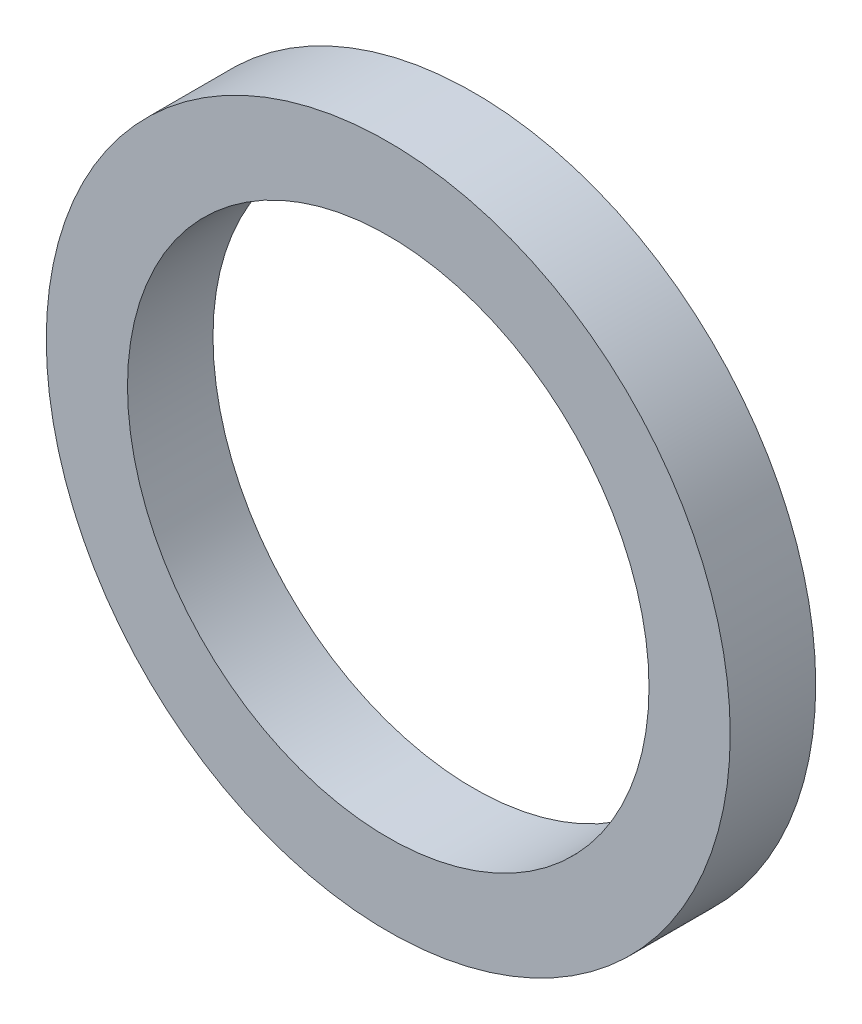
SolidWorks part; units mm, degrees
material "PVC hart"
ref_plane "Ebene vorne" through (0, 0, 0) normal (0, 0, 1) x (1, 0, 0)
ref_plane "Ebene oben" through (0, 0, 0) normal (0, 1, 0) x (1, 0, 0)
ref_plane "Ebene rechts" through (0, 0, 0) normal (1, 0, 0) x (0, 0, -1)
sketch "Skizze2" plane through (0, 0, 0) normal (0, 0, 1) x (1, 0, 0)
  circle A0 centre (0, 0) radius 3.05
  circle A1 centre (0, 0) radius 4
  dimension "D1" = 6.1
  dimension "D2" = 8
extrude "Aufsatz-Linear austragen1" add sketch "Skizze2" against normal blind 1
